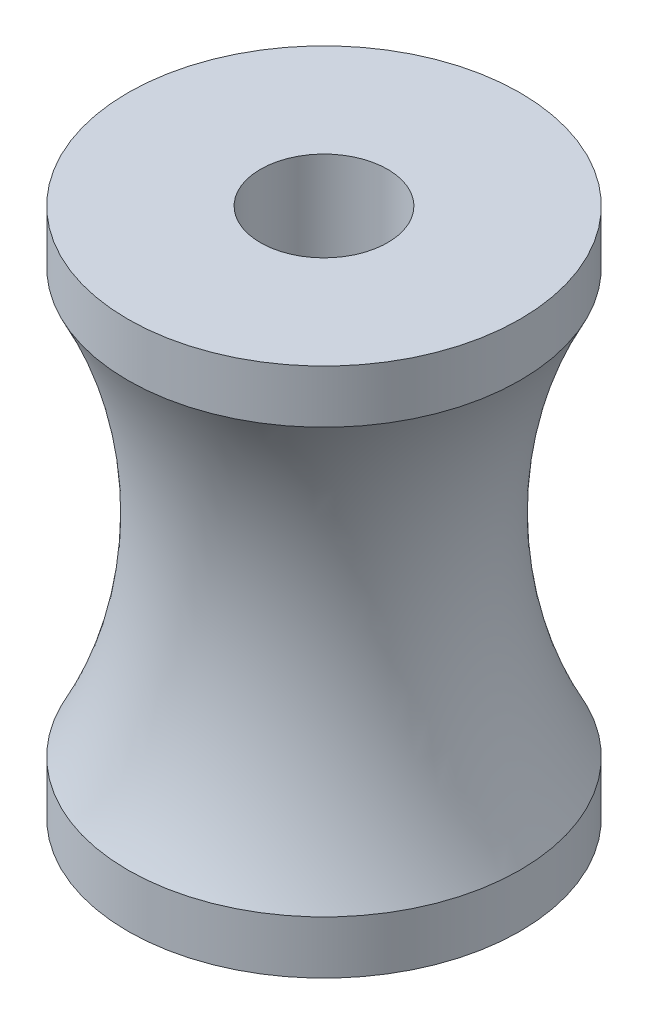
SolidWorks part; units mm, degrees
ref_plane "Front Plane" through (0, 0, 0) normal (0, 0, 1) x (1, 0, 0)
ref_plane "Top Plane" through (0, 0, 0) normal (0, 1, 0) x (1, 0, 0)
ref_plane "Right Plane" through (0, 0, 0) normal (1, 0, 0) x (0, 0, -1)
sketch "Sketch1" plane through (0, 0, 0) normal (0, 0, 1) x (1, 0, 0)
  line L0 (0, 500) -> (0, -500) construction
  line L1 (-120, 500) -> (-370, 500)
  line L2 (-370, 500) -> (-370, 400)
  line L3 (-120, -500) -> (-370, -500)
  line L4 (-370, -500) -> (-370, -400)
  line L5 (-120, 500) -> (-120, -500)
  arc A0 (-370, 400) -> (-370, -400) centre (-1131.3147, 0) cw
  point P3 (0, 0)
  dimension "D2" = 100
  dimension "D4" = 860
  dimension "D1" = 1000
  dimension "D3" = 100
  dimension "D5" = 250
  dimension "D6" = 250
  dimension "D7" = 120
revolve "Revolve1" add sketch "Sketch1" angle 360 about L0
